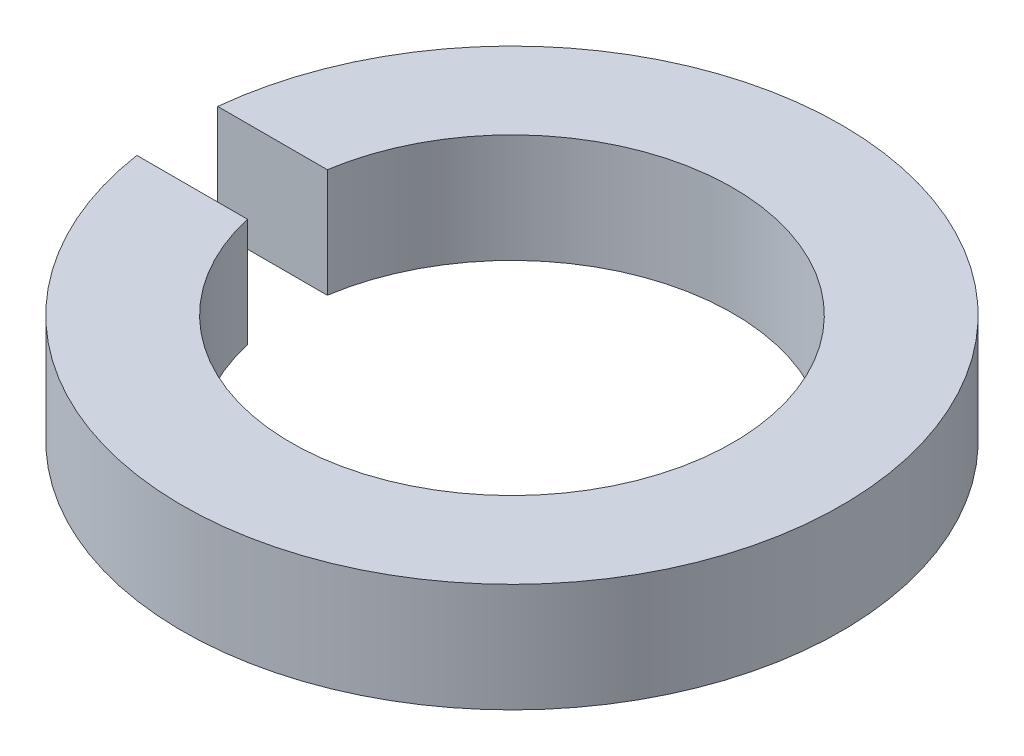
SolidWorks part; units mm, degrees
material "AISI 304"
ref_plane "前视基准面" through (0, 0, 0) normal (0, 0, 1) x (1, 0, 0)
ref_plane "上视基准面" through (0, 0, 0) normal (0, 1, 0) x (1, 0, 0)
ref_plane "右视基准面" through (0, 0, 0) normal (1, 0, 0) x (0, 0, -1)
sketch "草图1" plane through (0, 0, 0) normal (0, 1, 0) x (1, 0, 0)
  line L0 (-1.606, 0.2478) -> (-2.4123, 0.2478)
  line L1 (-2.3979, -0.3613) -> (-1.5843, -0.3613)
  arc A0 (-2.3979, -0.3613) -> (-2.4123, 0.2478) centre (0, 0) ccw
  arc A1 (-1.5843, -0.3613) -> (-1.606, 0.2478) centre (0, 0) ccw
  dimension "D1" = 0.8
  dimension "D2" = 3.25
extrude "凸台-拉伸1" add sketch "草图1" along normal blind 0.8
